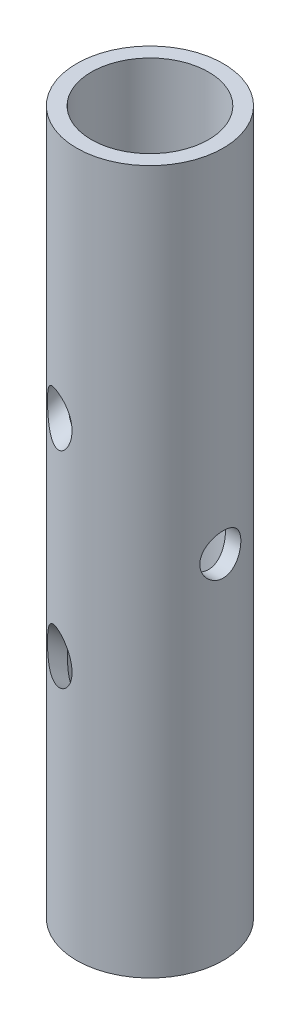
SolidWorks part; units mm, degrees
ref_plane "前视基准面" through (0, 0, 0) normal (0, 0, 1) x (1, 0, 0)
ref_plane "上视基准面" through (0, 0, 0) normal (0, 1, 0) x (1, 0, 0)
ref_plane "右视基准面" through (0, 0, 0) normal (1, 0, 0) x (0, 0, -1)
sketch "草图1" plane through (0, 0, 0) normal (0, 1, 0) x (1, 0, 0)
  circle A0 centre (0, 0) radius 12.5
  circle A1 centre (0, 0) radius 10
  dimension "D1" = 25
  dimension "D2" = 20
extrude "凸台-拉伸1" add sketch "草图1" along normal blind 120
sketch "草图2" plane through (0, 0, 0) normal (1, 0, 0) x (0, 0, -1)
  line L0 (-12.5, 60) -> (12.5, 60) construction
  line L1 (-12.5, 120) -> (-12.5, 0) construction
  line L2 (12.5, 0) -> (12.5, 120) construction
  line L3 (0, 120) -> (0, 0) construction
  line L4 (10, 120) -> (-10, 120) construction
  circle A0 centre (0, 60) radius 3.5
  dimension "D1" = 7
extrude "切除-拉伸1" cut sketch "草图2" along normal mid plane 25
sketch "草图3" plane through (0, 0, 0) normal (0, 1, 0) x (1, 0, 0)
  line L0 (-12.5, 0) -> (12.5, 0) construction
  line L2 (-5.7844, -15.8924) -> (5.7844, 15.8924) construction
  circle A0 centre (0, 0) radius 12.5 construction
  dimension "D1" = 110
sketch "草图7" plane through (0, 0, 0) normal (0, 0, 1) x (1, 0, 0)
  line L1 (-12.5, 120) -> (-12.5, 0) construction
ref_plane "基准面2" through (0, 0, 0) normal (0.9397, 0, 0.342) x (0.342, 0, -0.9397)
sketch "草图10" plane through (0, 0, 0) normal (0.9397, 0, 0.342) x (0.342, 0, -0.9397)
  line L0 (-12.5, 0) -> (-12.5, 120) construction
  line L1 (-12.5, 60) -> (12.5, 60) construction
  line L2 (12.5, 0) -> (12.5, 120) construction
  line L3 (-37.5, 60) -> (42.4943, 116.0126)
  line L4 (-37.5, 60) -> (79.1818, -21.7015)
  line L5 (-12.5, 60) -> (-37.5, 60) construction
  point P10 (-37.3466, 60)
  point P12 (0, 0)
  point P14 (-41.4697, 60)
  dimension "D1" = 35
  dimension "D2" = 35
  dimension "D3" = 25
sweep "切除-扫描3" cut path "草图10" circular profile diameter 7 parameters "D3"=7
ref_plane "基准面3" through (-4.2753, 0, 11.7462) normal (-0.342, 0, 0.9397) x (0.9397, 0, 0.342)
